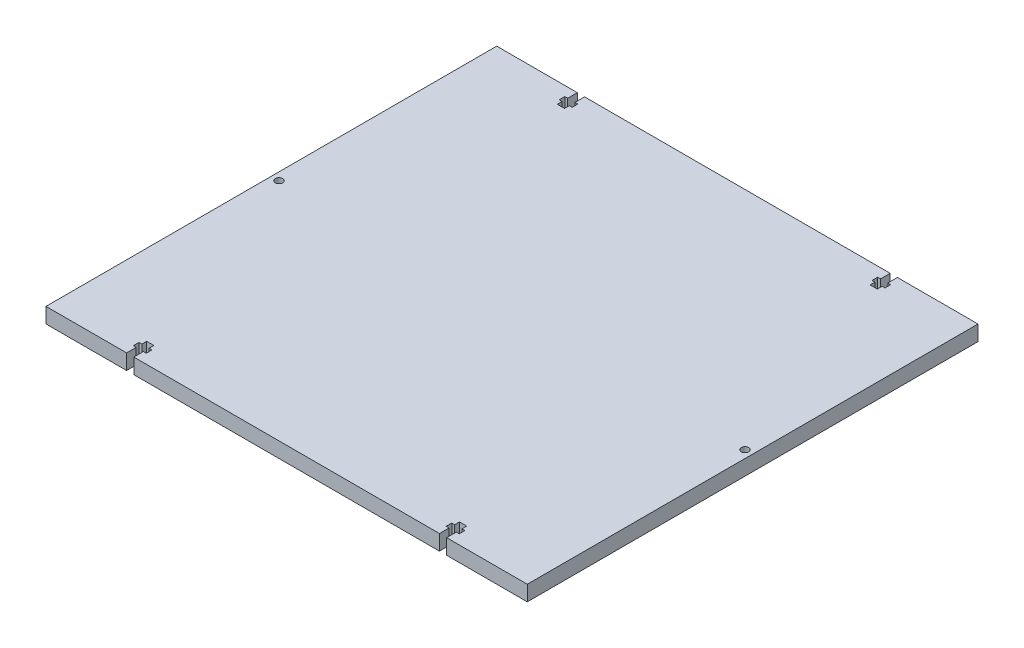
SolidWorks part; units mm, degrees
ref_plane "Front" through (0, 0, 0) normal (0, 0, 1) x (1, 0, 0)
ref_plane "Top" through (0, 0, 0) normal (0, 1, 0) x (1, 0, 0)
ref_plane "Right" through (0, 0, 0) normal (1, 0, 0) x (0, 0, -1)
sketch "Sketch1" plane through (0, 0, 0) normal (0, 1, 0) x (1, 0, 0)
  line L1 (100, -93.65) -> (-100, -93.65)
  line L2 (100, -93.65) -> (100, 93.65)
  line L3 (100, 93.65) -> (-100, 93.65)
  line L4 (-100, -93.65) -> (-100, 93.65)
  line L5 (100, -93.65) -> (-100, 93.65) construction
  line L6 (100, 93.65) -> (-100, -93.65) construction
  point P0 (0, 0)
  dimension "D1" = 200
  dimension "D2" = 187.3
extrude "Boss-Extrude1" add sketch "Sketch1" along normal blind 6.35
sketch "Sketch2" plane through (0, 6.35, 0) normal (0, 1, 0) x (1, 0, 0)
  line L12 (0, -93.65) -> (0, 93.65) construction
  line L25 (100, 93.65) -> (-100, 93.65) construction
  line L38 (-63.5, 87.3) -> (-62.29, 87.3)
  line L39 (-66.5, 85.3) -> (-63.5, 85.3)
  line L40 (-63.5, 87.3) -> (-63.5, 85.3)
  line L41 (-66.5, 87.3) -> (-66.5, 85.3)
  line L42 (-67.71, 87.3) -> (-66.5, 87.3)
  line L43 (-62.29, 89.65) -> (-62.29, 87.3)
  line L44 (-67.71, 89.65) -> (-66.5, 89.65)
  line L45 (-67.71, 89.65) -> (-67.71, 87.3)
  line L46 (-63.5, 89.65) -> (-62.29, 89.65)
  line L47 (-63.5, 93.65) -> (-63.5, 89.65)
  line L48 (-66.5, 93.65) -> (-63.5, 93.65)
  line L49 (-66.5, 93.65) -> (-66.5, 89.65)
  line L74 (-100, -93.65) -> (100, -93.65) construction
  line L75 (-100, 93.65) -> (-93.65, 93.65) construction
  line L76 (-100, 93.65) -> (-100, -93.65) construction
  line L77 (-100, -93.65) -> (-93.65, -93.65) construction
  line L79 (66.5, 93.65) -> (66.5, 89.65)
  line L80 (66.5, 93.65) -> (63.5, 93.65)
  line L81 (63.5, 93.65) -> (63.5, 89.65)
  line L82 (63.5, 89.65) -> (62.29, 89.65)
  line L83 (67.71, 89.65) -> (67.71, 87.3)
  line L84 (67.71, 89.65) -> (66.5, 89.65)
  line L85 (62.29, 89.65) -> (62.29, 87.3)
  line L86 (67.71, 87.3) -> (66.5, 87.3)
  line L87 (66.5, 87.3) -> (66.5, 85.3)
  line L88 (63.5, 87.3) -> (63.5, 85.3)
  line L89 (66.5, 85.3) -> (63.5, 85.3)
  line L90 (63.5, 87.3) -> (62.29, 87.3)
  line L91 (-100, 0) -> (100, 0) construction
  line L92 (100, -93.65) -> (100, 93.65) construction
  line L93 (63.5, -87.3) -> (62.29, -87.3)
  line L94 (66.5, -85.3) -> (63.5, -85.3)
  line L95 (63.5, -87.3) -> (63.5, -85.3)
  line L96 (66.5, -87.3) -> (66.5, -85.3)
  line L97 (67.71, -87.3) -> (66.5, -87.3)
  line L98 (62.29, -89.65) -> (62.29, -87.3)
  line L99 (67.71, -89.65) -> (66.5, -89.65)
  line L100 (67.71, -89.65) -> (67.71, -87.3)
  line L101 (63.5, -89.65) -> (62.29, -89.65)
  line L102 (63.5, -93.65) -> (63.5, -89.65)
  line L103 (66.5, -93.65) -> (63.5, -93.65)
  line L104 (66.5, -93.65) -> (66.5, -89.65)
  line L105 (-66.5, -93.65) -> (-66.5, -89.65)
  line L106 (-66.5, -93.65) -> (-63.5, -93.65)
  line L107 (-63.5, -93.65) -> (-63.5, -89.65)
  line L108 (-63.5, -89.65) -> (-62.29, -89.65)
  line L109 (-67.71, -89.65) -> (-67.71, -87.3)
  line L110 (-67.71, -89.65) -> (-66.5, -89.65)
  line L111 (-62.29, -89.65) -> (-62.29, -87.3)
  line L112 (-67.71, -87.3) -> (-66.5, -87.3)
  line L113 (-66.5, -87.3) -> (-66.5, -85.3)
  line L114 (-63.5, -87.3) -> (-63.5, -85.3)
  line L115 (-66.5, -85.3) -> (-63.5, -85.3)
  line L116 (-63.5, -87.3) -> (-62.29, -87.3)
  circle A0 centre (-96.825, 0) radius 1.55
  circle A1 centre (96.825, 0) radius 1.55
  point P58 (-65, 85.3)
  dimension "D1" = 3.1
  dimension "D2" = 4
  dimension "D3" = 2.35
  dimension "D4" = 2
  dimension "D5" = 65
extrude "Cut-Extrude1" cut sketch "Sketch2" against normal through all
